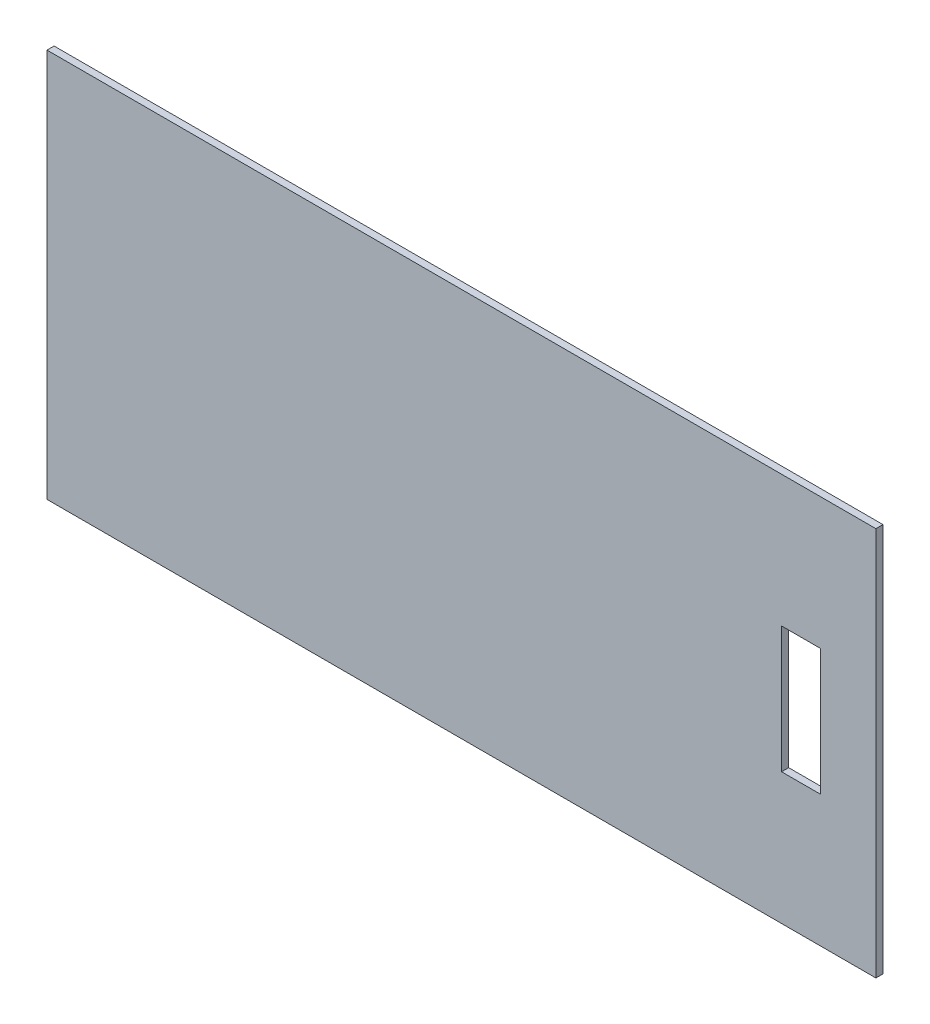
SolidWorks part; units mm, degrees
material "Acrylic (Medium-high impact)"
ref_plane "Front Plane" through (0, 0, 0) normal (0, 0, 1) x (1, 0, 0)
ref_plane "Top Plane" through (0, 0, 0) normal (0, 1, 0) x (1, 0, 0)
ref_plane "Right Plane" through (0, 0, 0) normal (1, 0, 0) x (0, 0, -1)
sketch "Sketch1" plane through (0, 0, 0) normal (0, 0, 1) x (1, 0, 0)
  line L1 (-192.3868, 71.9669) -> (216.6132, 71.9669)
  line L2 (-192.3868, 71.9669) -> (-192.3868, -120.0331)
  line L3 (-192.3868, -120.0331) -> (216.6132, -120.0331)
  line L4 (216.6132, 71.9669) -> (216.6132, -120.0331)
  dimension "D1" = 409
  dimension "D2" = 192
extrude "Boss-Extrude1" add sketch "Sketch1" along normal blind 3.5
sketch "Sketch2" plane through (0, 0, 3.5) normal (0, 0, 1) x (1, 0, 0)
  line L0 (216.6132, -120.0331) -> (216.6132, 71.9669) construction
  line L1 (170.0632, 7.1169) -> (189.2632, 7.1169)
  line L2 (170.0632, 7.1169) -> (170.0632, -55.1831)
  line L3 (170.0632, -55.1831) -> (189.2632, -55.1831)
  line L4 (189.2632, 7.1169) -> (189.2632, -55.1831)
  line L6 (216.6132, 71.9669) -> (-192.3868, 71.9669) construction
  point P6 (189.2632, -24.0331)
  dimension "D1" = 62.3
  dimension "D2" = 19.2
  dimension "D3" = 27.35
  dimension "D4" = 96
extrude "Cut-Extrude1" cut sketch "Sketch2" against normal through all
